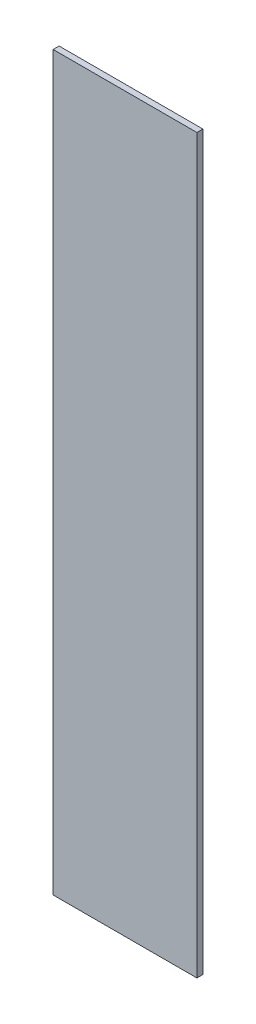
SolidWorks part; units mm, degrees
ref_plane "Front Plane" through (0, 0, 0) normal (0, 0, 1) x (1, 0, 0)
ref_plane "Top Plane" through (0, 0, 0) normal (0, 1, 0) x (1, 0, 0)
ref_plane "Right Plane" through (0, 0, 0) normal (1, 0, 0) x (0, 0, -1)
sketch "Sketch1" plane through (0, 0, 0) normal (0, 0, 1) x (1, 0, 0)
  line L1 (0, 0) -> (432, 0)
  line L2 (0, 0) -> (0, 2200)
  line L3 (0, 2200) -> (432, 2200)
  line L4 (432, 0) -> (432, 2200)
  dimension "D1" = 2200
  dimension "D2" = 432
extrude "Boss-Extrude1" add sketch "Sketch1" along normal blind 18
